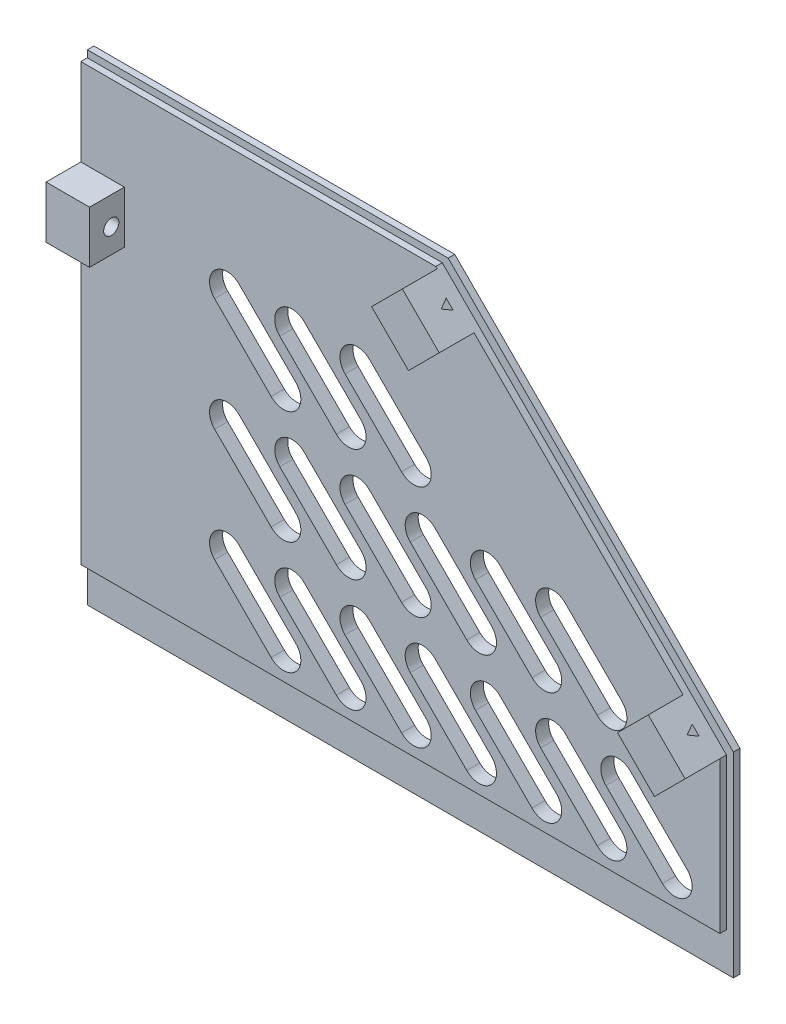
SolidWorks part; units mm, degrees
material "ABS"
ref_plane "Front" through (0, 0, 0) normal (0, 0, 1) x (1, 0, 0)
ref_plane "Top" through (0, 0, 0) normal (0, 1, 0) x (1, 0, 0)
ref_plane "Right" through (0, 0, 0) normal (1, 0, 0) x (0, 0, -1)
sketch "Croquis1" plane through (0, 0, 0) normal (0, 0, 1) x (1, 0, 0)
  line L0 (74.3, 0) -> (-74.3, 0)
  line L1 (-74.3, 0) -> (-74.3, 110.6)
  line L2 (-74.3, 110.6) -> (8.7, 110.6)
  line L3 (8.7, 110.6) -> (74.3, 45)
  line L4 (74.3, 45) -> (74.3, 0)
  dimension "D1" = 148.6
  dimension "D2" = 110.6
  dimension "D3" = 45
  dimension "D4" = 45
extrude "Saliente-Extruir1" add sketch "Croquis1" along normal blind 1.5
sketch "Croquis2" plane through (0, 0, 1.5) normal (0, 0, 1) x (1, 0, 0)
  line L0 (-74.3, 109) -> (-74.3, 8.8)
  line L1 (-74.3, 8.8) -> (72.7, 8.8)
  line L2 (72.7, 8.8) -> (72.7, 43.6302)
  line L3 (72.7, 43.6302) -> (7.3302, 109)
  line L4 (7.3302, 109) -> (-74.3, 109)
  line L6 (-74.3, 0) -> (74.3, 0) construction
  line L7 (74.3, 0) -> (74.3, 45) construction
  line L8 (-74.3, 110.6) -> (-74.3, 0) construction
  line L9 (8.7, 110.6) -> (-74.3, 110.6) construction
  line L10 (74.3, 45) -> (8.7, 110.6) construction
  dimension "D1" = 8.8
  dimension "D2" = 1.6
  dimension "D3" = 1.6
  dimension "D4" = 2.1
extrude "Saliente-Extruir2" add sketch "Croquis2" along normal blind 1.5
sketch "Croquis3" plane through (0, 0, 0) normal (0, 0, 1) x (1, 0, 0)
  line L0 (49.3, 28) -> (62.3, 15) construction
  line L1 (52.1284, 30.8284) -> (65.1284, 17.8284)
  line L2 (46.4716, 25.1716) -> (59.4716, 12.1716)
  line L3 (-74.3, 0) -> (74.3, 0) construction
  line L6 (74.3, 45) -> (8.7, 110.6) construction
  line L8 (74.3, 0) -> (74.3, 45) construction
  arc A0 (52.1284, 30.8284) -> (46.4716, 25.1716) centre (49.3, 28) ccw
  arc A1 (59.4716, 12.1716) -> (65.1284, 17.8284) centre (62.3, 15) ccw
  point P2 (55.8, 21.5)
  dimension "D1" = 8
  dimension "D2" = 15
  dimension "D3" = 13
  dimension "D4" = 12
extrude "ventilacion" cut sketch "Croquis3" along normal up to next (3 mm away)
pattern_linear "MatrizL1" count 7 spacing 15 along (-1, 0, 0) count 3 spacing 26 along (0, 1, 0) skipping (0, 1), (0, 2), (1, 2), (2, 2), (3, 2) of "ventilacion"
sketch "Croquis4" plane through (0, 0, 3) normal (0, 0, 1) x (1, 0, 0)
  line L0 (-74.3, 109) -> (-74.3, 8.8) construction
  line L1 (-74.3, 89) -> (-64.3, 89)
  line L2 (-74.3, 89) -> (-74.3, 77)
  line L3 (-74.3, 77) -> (-64.3, 77)
  line L4 (-64.3, 89) -> (-64.3, 77)
  line L5 (-74.3, 0) -> (74.3, 0) construction
  dimension "D1" = 12
  dimension "D2" = 10
  dimension "D3" = 77
extrude "Saliente-Extruir3" add sketch "Croquis4" along normal blind 8
sketch "Croquis5" plane through (-74.3, 0, 0) normal (-1, 0, 0) x (0, 0, 1)
  line L0 (0, 110.6) -> (0, 0) construction
  circle A0 centre (6, 82.6) radius 1.75
  dimension "D1" = 3.5
  dimension "D2" = 6
  dimension "D3" = 82.6
extrude "fix-sup" cut sketch "Croquis5" against normal up to next
sketch "Croquis6" plane through (0, 0, 3) normal (0, 0, 1) x (1, 0, 0)
  line L5 (72.7, 43.6302) -> (64.2147, 52.1154)
  line L6 (72.7, 43.6302) -> (7.3302, 109) construction
  line L7 (64.2147, 52.1154) -> (57.1437, 45.0444)
  line L8 (57.1437, 45.0444) -> (65.6289, 36.5591)
  line L9 (65.6289, 36.5591) -> (72.7, 43.6302)
  dimension "D1" = 12
  dimension "D2" = 10
extrude "Saliente-Extruir4" add sketch "Croquis6" along normal blind 8
sketch "Croquis7" plane through (58.1651, 58.1651, 0) normal (0.7071, 0.7071, 0) x (0, 0, -1)
  line L0 (-11, -20.5555) -> (-11, -8.5555) construction
  line L1 (-4.35, -13.4297) -> (-6.3, -14.5555)
  line L2 (-6.3, -14.5555) -> (-4.35, -15.6813)
  line L3 (-4.35, -15.6813) -> (-4.35, -13.4297)
  line L4 (0, -20.7182) -> (0, 72.0542) construction
  circle A0 centre (-5, -14.5555) radius 1.3 construction
  point P8 (-11, -14.5555)
  dimension "D1" = 5
  dimension "D2" = 2.6
extrude "Cortar-Extruir4" cut sketch "Croquis7" against normal up to next (10 mm away)
ref_plane "Plano1" through (-18.15, 18.15, 0) normal (-0.7071, 0.7071, 0) x (0.7071, 0.7071, 0)
pattern_linear "MatrizL2" count 2 spacing 80 along (-0.7071, 0.7071, 0) of "Saliente-Extruir4", "Cortar-Extruir4"
